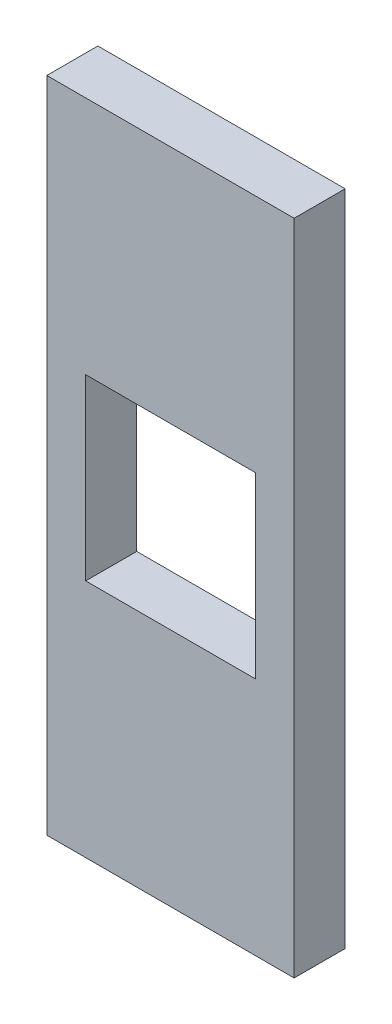
SolidWorks part; units mm, degrees
ref_plane "Front Plane" through (0, 0, 0) normal (0, 0, 1) x (1, 0, 0)
ref_plane "Top Plane" through (0, 0, 0) normal (0, 1, 0) x (1, 0, 0)
ref_plane "Right Plane" through (0, 0, 0) normal (1, 0, 0) x (0, 0, -1)
sketch "Sketch1" plane through (0, 0, 0) normal (0, 0, 1) x (1, 0, 0)
  line L0 (0, 66.85) -> (0, 44.55) construction
  line L1 (0, 66.85) -> (25, 66.85) construction
  line L2 (0, 44.55) -> (0, 39.4) construction
  line L3 (25, 0) -> (0, 0) construction
  line L4 (3.96, 42.425) -> (21.04, 42.425) construction
  line L5 (3.96, 24.425) -> (21.04, 24.425) construction
  line L6 (3.96, 42.425) -> (3.96, 24.425) construction
  line L7 (21.04, 42.425) -> (21.04, 24.425) construction
  line L8 (0, 44.55) -> (25, 44.55) construction
  line L9 (0, 39.4) -> (25, 39.4) construction
  line L10 (0, 39.4) -> (0, 27.45) construction
  line L11 (0, 27.45) -> (0, 22.3) construction
  line L12 (25, 44.55) -> (25, 39.4) construction
  line L13 (25, 66.85) -> (25, 44.55) construction
  line L14 (0, 22.3) -> (0, 0) construction
  line L15 (25, 39.4) -> (25, 27.45) construction
  line L16 (25, 27.45) -> (25, 22.3) construction
  line L17 (25, 22.3) -> (25, 0) construction
  line L18 (0, 27.45) -> (25, 27.45) construction
  line L19 (25, 22.3) -> (0, 22.3) construction
  line L20 (12.5, -0.0005) -> (12.5, 4.0956) construction
  line L21 (-0.1, 66.95) -> (25.1, 66.95)
  line L22 (25.1, 66.95) -> (25.1, 44.55)
  line L23 (25.1, 44.55) -> (25.1, 39.4)
  line L24 (25.1, 39.4) -> (25.1, 27.45)
  line L25 (25.1, 27.45) -> (25.1, 22.3)
  line L26 (25.1, 22.3) -> (25.1, -0.1)
  line L27 (25.1, -0.1) -> (-0.1, -0.1)
  line L28 (-0.1, 22.3) -> (-0.1, -0.1)
  line L29 (-0.1, 27.45) -> (-0.1, 22.3)
  line L30 (-0.1, 39.4) -> (-0.1, 27.45)
  line L31 (-0.1, 44.55) -> (-0.1, 39.4)
  line L32 (-0.1, 66.95) -> (-0.1, 44.55)
  line L33 (3.86, 42.525) -> (3.86, 24.325)
  line L34 (3.86, 24.325) -> (21.14, 24.325)
  line L35 (21.14, 42.525) -> (21.14, 24.325)
  line L36 (3.86, 42.525) -> (21.14, 42.525)
  point P18 (12.5, 24.425)
  point P20 (12.5, 42.425)
  point P21 (12.5, 66.85)
  dimension "D1" = 22.3
  dimension "D2" = 11.95
  dimension "D3" = 5.15
  dimension "D4" = 25
  dimension "D5" = 18
  dimension "D6" = 17.08
  dimension "D7" = 3.025
  dimension "D8" = 0.1
  dimension "D9" = 0.1
extrude "Boss-Extrude1" add sketch "Sketch1" along normal blind 5.2
